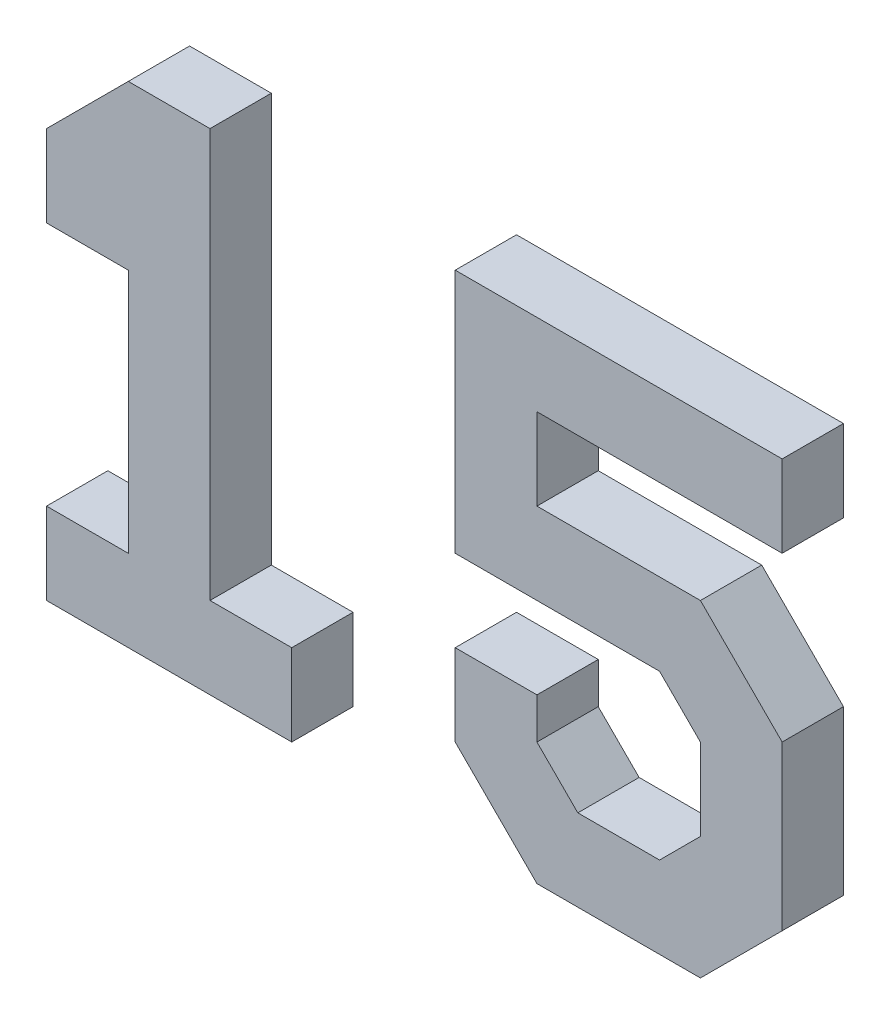
SolidWorks part; units mm, degrees
ref_plane "Front" through (0, 0, 0) normal (0, 0, 1) x (1, 0, 0)
ref_plane "Top" through (0, 0, 0) normal (0, 1, 0) x (1, 0, 0)
ref_plane "Right" through (0, 0, 0) normal (1, 0, 0) x (0, 0, -1)
sketch "Sketch1" plane through (0, 0, 0) normal (0, 0, 1) x (1, 0, 0)
  line L0 (0, 0) -> (60, 0)
  line L1 (0, 0) -> (0, 20)
  line L2 (0, 0) -> (0, 20)
  line L3 (0, 80) -> (0, 100)
  line L4 (180, 20) -> (180, 60)
  line L5 (0, 20) -> (20, 20)
  line L6 (120, 100) -> (180, 100)
  line L7 (40, 20) -> (60, 20)
  line L8 (120, 80) -> (160, 80)
  line L9 (120, 80) -> (120, 100)
  line L11 (0, 80) -> (20, 80)
  line L12 (120, 30) -> (120, 40)
  line L13 (130, 20) -> (150, 20)
  line L14 (150, 20) -> (160, 30)
  line L16 (20, 20) -> (20, 80)
  line L17 (100, 60) -> (100, 120)
  line L18 (40, 20) -> (40, 120)
  line L20 (60, 0) -> (60, 20)
  line L22 (100, 20) -> (100, 40)
  line L27 (160, 30) -> (160, 50)
  line L30 (20, 120) -> (40, 120)
  line L31 (20, 120) -> (40, 120)
  line L32 (20, 120) -> (0, 100)
  line L33 (180, 20) -> (160, 0)
  line L34 (120, 0) -> (100, 20)
  line L35 (120, 30) -> (130, 20)
  line L36 (180, 60) -> (160, 80)
  line L37 (150, 60) -> (160, 50)
  line L38 (180, 100) -> (180, 120)
  line L44 (120, 0) -> (160, 0)
  line L49 (100, 40) -> (120, 40)
  line L51 (100, 60) -> (150, 60)
  line L57 (100, 120) -> (180, 120)
  line L79 (70, 0) -> (70, 120) [skipped]
  line L80 (80, 0) -> (80, 120) [skipped]
  line L81 (90, 0) -> (90, 120) [skipped]
  line L82 (10, 10) -> (10, 20) [skipped]
  line L83 (50, 10) -> (50, 20) [skipped]
  line L89 (30, 90) -> (30, 110) [skipped]
  line L90 (150, 30) -> (150, 50) [skipped]
  line L91 (140, 30) -> (140, 40) [skipped]
  line L92 (130, 30) -> (130, 40) [skipped]
  line L93 (110, 20) -> (110, 30) [skipped]
  line L96 (170, 30) -> (170, 60) [skipped]
  line L102 (0, 0) -> (0, 20) [skipped]
  line L103 (120, 10) -> (120, 20) [skipped]
  line L104 (100, 0) -> (100, 10) [skipped]
  line L105 (160, 10) -> (160, 20) [skipped]
extrude "Extrude1" add sketch "Sketch1" along normal blind 15 contours L30 L32 L3 L11 L16 L5 L1 L0 L20 L7 L18 | L57 L17 L51 L37 L27 L14 L13 L35 L12 L49 L22 L34 L44 L33 L4 L36 L8 L9 L6 L38
